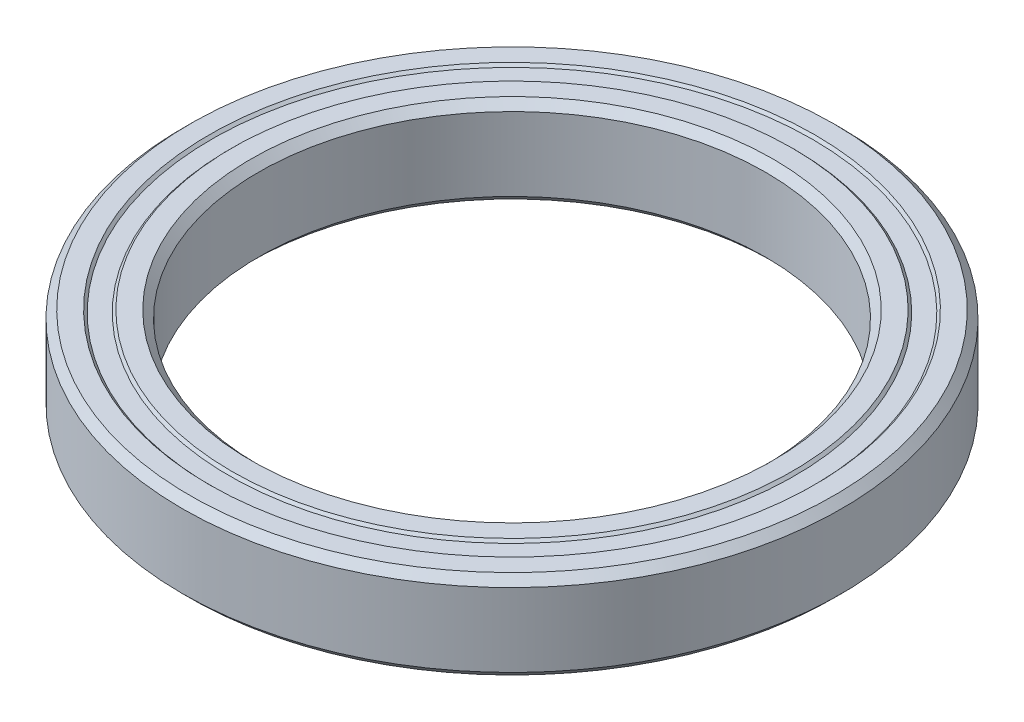
SolidWorks part; units mm, degrees
material "Stainless Steel (ferritic)"
ref_plane "Front Plane" through (0, 0, 0) normal (0, 0, 1) x (1, 0, 0)
ref_plane "Top Plane" through (0, 0, 0) normal (0, 1, 0) x (1, 0, 0)
ref_plane "Right Plane" through (0, 0, 0) normal (1, 0, 0) x (0, 0, -1)
sketch "Sketch1" plane through (0, 0, 0) normal (0, 0, 1) x (1, 0, 0)
  line L0 (0, -1.3494) -> (0, 70.5256) construction
  line L1 (20, 2.9) -> (20, -2.9)
  line L2 (20, -2.9) -> (20.6, -3.5)
  line L3 (20.6, -3.5) -> (22.1, -3.5)
  line L4 (22.1, -3.5) -> (22.3, -3.3)
  line L5 (22.3, -3.3) -> (23.7, -3.3)
  line L6 (23.7, -3.3) -> (23.9, -3.5)
  line L7 (23.9, -3.5) -> (25.4, -3.5)
  line L8 (25.4, -3.5) -> (26, -2.9)
  line L9 (26, -2.9) -> (26, 2.9)
  line L10 (26, 2.9) -> (25.4, 3.5)
  line L11 (25.4, 3.5) -> (23.9, 3.5)
  line L12 (23.9, 3.5) -> (23.7, 3.3)
  line L13 (23.7, 3.3) -> (22.3, 3.3)
  line L14 (22.3, 3.3) -> (22.1, 3.5)
  line L15 (22.1, 3.5) -> (20.6, 3.5)
  line L16 (20.6, 3.5) -> (20, 2.9)
  line L17 (0, 0) -> (20, 0) construction
  dimension "D1" = 20
  dimension "D2" = 7
  dimension "D3" = 0.6
  dimension "D4" = 0.2
  dimension "D5" = 26
  dimension "D6" = 1.5
revolve "Revolve1" add sketch "Sketch1" angle 360 about L0
